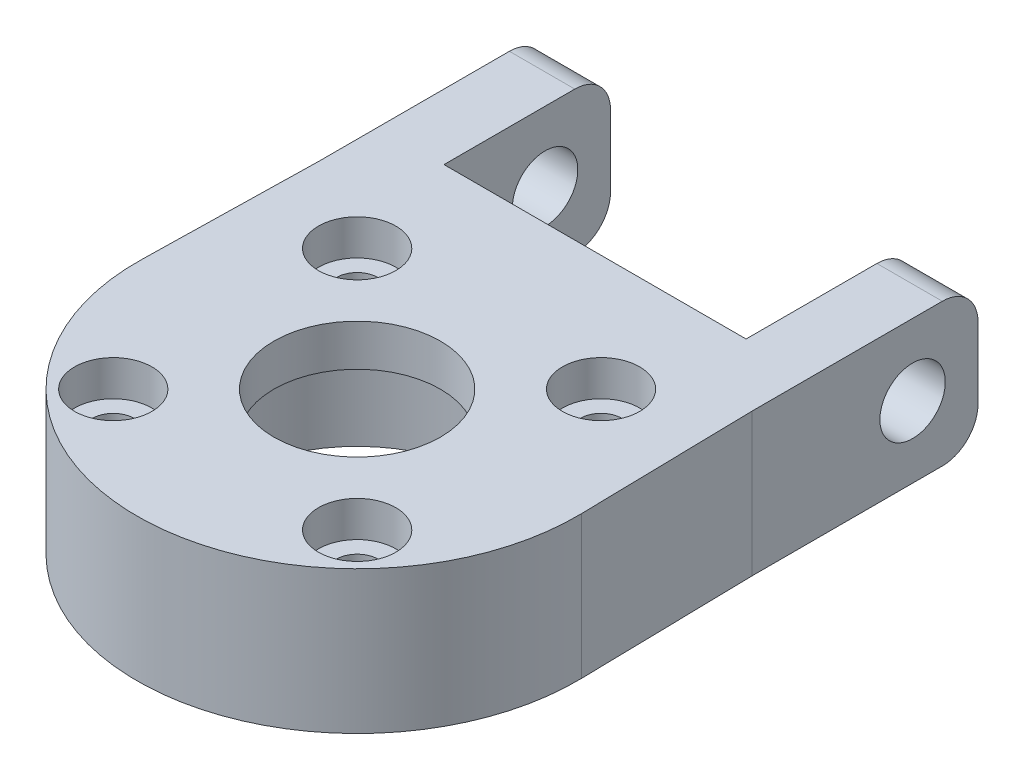
SolidWorks part; units mm, degrees
ref_plane "Front Plane" through (0, 0, 0) normal (0, 0, 1) x (1, 0, 0)
ref_plane "Top Plane" through (0, 0, 0) normal (0, 1, 0) x (1, 0, 0)
ref_plane "Right Plane" through (0, 0, 0) normal (1, 0, 0) x (0, 0, -1)
sketch "Sketch1" plane through (0, 0, 0) normal (0, 1, 0) x (1, 0, 0)
  line L0 (0, 0) -> (0, 15) construction
  line L1 (-18.2, 15) -> (18.2, 15) construction
  line L2 (-18.2, 15) -> (-18.2, 20)
  line L3 (-18.2, 20) -> (18.2, 20)
  line L4 (18.2, 20) -> (18.2, 15)
  line L5 (-18.2, 15) -> (-18.4962, 0.3746)
  line L6 (18.2, 15) -> (18.4962, 0.3746)
  circle A0 centre (0, 0) radius 7
  circle A1 centre (0, 0) radius 18.5 construction
  arc A2 (-18.4962, 0.3746) -> (18.4962, 0.3746) centre (0, 0) ccw
  point P8 (0, 15)
  dimension "D1" = 14
  dimension "D2" = 37
  dimension "D3" = 15
  dimension "D4" = 5
  dimension "D5" = 36.4
extrude "Boss-Extrude1" add sketch "Sketch1" along normal blind 12
sketch "Sketch2" plane through (0, 0, 0) normal (0, -1, 0) x (1, 0, 0)
  circle A0 centre (0, 0) radius 11.075
  dimension "D1" = 22.15
extrude "Cut-Extrude1" cut sketch "Sketch2" against normal blind 8.5
sketch "Sketch4" plane through (0, 0, 0) normal (0, -1, 0) x (1, 0, 0)
  line L0 (0, 0) -> (10.253, 10.253) construction
  line L1 (0, 0) -> (0, 5.0875) construction
  circle A1 centre (10.253, 10.253) radius 1.75
  circle A2 centre (10.253, -10.253) radius 1.75
  circle A3 centre (-10.253, -10.253) radius 1.75
  circle A4 centre (-10.253, 10.253) radius 1.75
  point P15 (0, 0)
  dimension "D1" = 45
  dimension "D2" = 3.5
  dimension "D3" = 14.5
  dimension "D4" = 4
extrude "Cut-Extrude4" cut sketch "Sketch4" against normal through all
sketch "Sketch5" plane through (0, 12, 0) normal (0, 1, 0) x (1, 0, 0)
  circle A0 centre (-10.253, 10.253) radius 3.25
  circle A1 centre (10.253, 10.253) radius 3.25
  circle A2 centre (10.253, -10.253) radius 3.25
  circle A3 centre (-10.253, -10.253) radius 3.25
  point P12 (0, 0)
  dimension "D1" = 6.5
  dimension "D2" = 4
extrude "Cut-Extrude5" cut sketch "Sketch5" against normal blind 3
sketch "Sketch6" plane through (0, 0, -20) normal (0, 0, -1) x (-1, 0, 0)
  line L0 (-18.2, 12) -> (18.2, 12) construction
  line L1 (-18.2, 0) -> (-12.7, 0)
  line L2 (-18.2, 0) -> (-18.2, 12)
  line L3 (-18.2, 12) -> (-12.7, 12)
  line L4 (-12.7, 0) -> (-12.7, 12)
  line L5 (0, 0) -> (0, 7.3385) construction
  line L6 (-18.2, 0) -> (18.2, 0) construction
  line L10 (12.7, 0) -> (12.7, 12)
  line L11 (18.2, 12) -> (12.7, 12)
  line L12 (18.2, 0) -> (18.2, 12)
  line L13 (18.2, 0) -> (12.7, 0)
extrude "Boss-Extrude2" add sketch "Sketch6" along normal blind 14
sketch "Sketch7" plane through (-18.2, 0, 0) normal (-1, 0, 0) x (0, 0, 1)
  line L0 (-34, 6) -> (-28.5011, 6) construction
  line L1 (-34, 0) -> (-34, 12) construction
  circle A0 centre (-28.5011, 6) radius 2.75
  dimension "D1" = 5.5
extrude "Cut-Extrude6" cut sketch "Sketch7" against normal through all contours A0
fillet "Fillet1" radius 3 4 edges at (15.45, 0, -34) (15.45, 12, -34) (-15.45, 12, -34) (-15.45, 0, -34)
